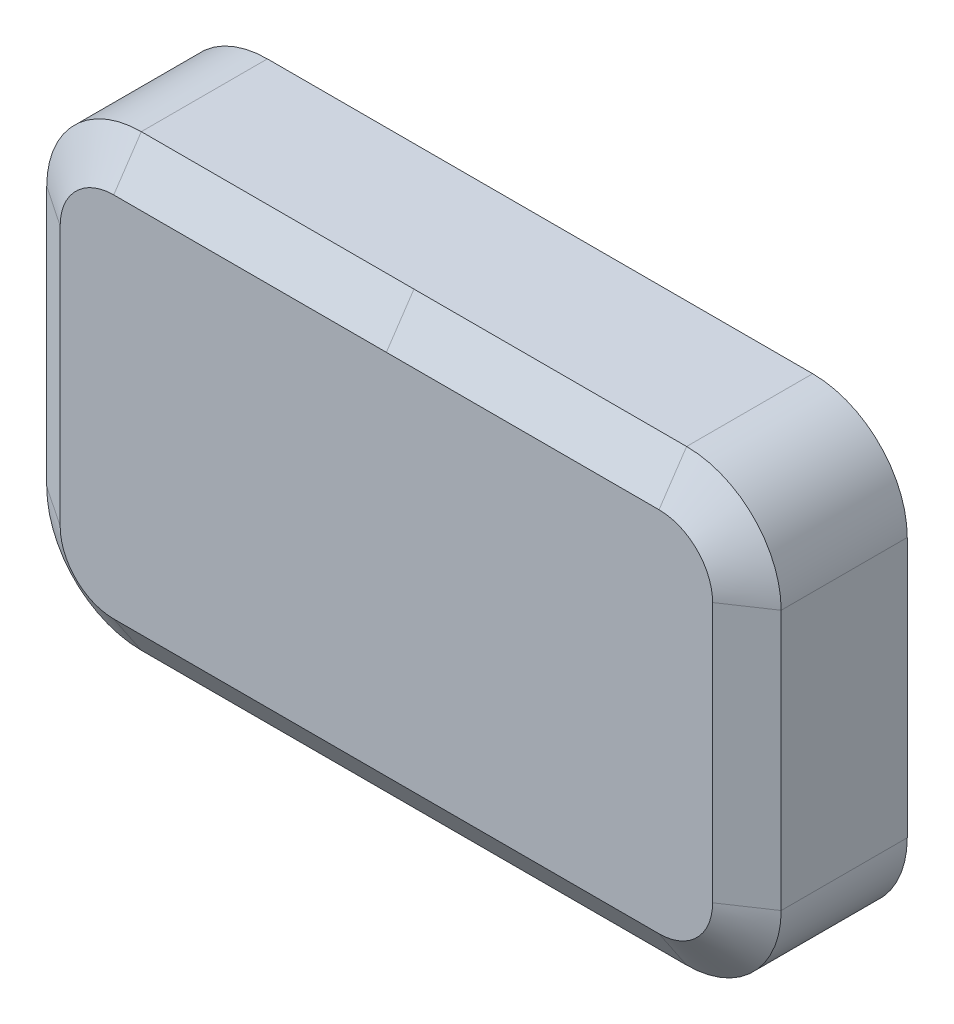
SolidWorks part; units mm, degrees
ref_plane "Front Plane" through (0, 0, 0) normal (0, 0, 1) x (1, 0, 0)
ref_plane "Top Plane" through (0, 0, 0) normal (0, 1, 0) x (1, 0, 0)
ref_plane "Right Plane" through (0, 0, 0) normal (1, 0, 0) x (0, 0, -1)
sketch "Sketch1" plane through (0, 0, 0) normal (0, 0, 1) x (1, 0, 0)
  line L1 (59.182, -36.195) -> (-59.182, -36.195)
  line L2 (59.182, -36.195) -> (59.182, 36.195)
  line L3 (59.182, 36.195) -> (-59.182, 36.195)
  line L4 (-59.182, -36.195) -> (-59.182, 36.195)
  line L5 (59.182, -36.195) -> (-59.182, 36.195) construction
  line L6 (59.182, 36.195) -> (-59.182, -36.195) construction
  point P0 (0, 0)
  dimension "D1" = 118.364
  dimension "D2" = 72.39
extrude "Boss-Extrude1" add sketch "Sketch1" along normal blind 27.94
sketch "Sketch2" plane through (0, 0, 0) normal (0, 0, -1) x (-1, 0, 0)
  line L1 (43.434, -21.717) -> (-43.434, -21.717) construction
  line L2 (43.434, -21.717) -> (43.434, 21.717) construction
  line L3 (43.434, 21.717) -> (-43.434, 21.717) construction
  line L4 (-43.434, -21.717) -> (-43.434, 21.717) construction
  line L5 (43.434, -21.717) -> (-43.434, 21.717) construction
  line L6 (43.434, 21.717) -> (-43.434, -21.717) construction
  circle A0 centre (-43.434, 21.717) radius 4.318
  circle A1 centre (-43.434, -21.717) radius 4.318
  circle A2 centre (43.434, -21.717) radius 4.318
  circle A3 centre (43.434, 21.717) radius 4.318
  point P0 (0, 0)
  point P11 (33.3654, 17.664)
  dimension "D1" = 8.636
  dimension "D2" = 86.868
  dimension "D3" = 43.434
extrude "Boss-Extrude2" add sketch "Sketch2" along normal blind 1.9558 draft 15
fillet "Fillet1" radius 15.24 4 edges at (-59.182, 36.195, 13.97) (-59.182, -36.195, 13.97) (59.182, -36.195, 13.97) (59.182, 36.195, 13.97)
sketch "Sketch3" plane through (0, 0, 0) normal (1, 0, 0) x (0, 0, -1)
  line L0 (-23.495, 36.195) -> (-27.94, 29.591)
  line L1 (-27.94, 36.195) -> (0, 36.195) construction
  line L2 (-27.94, -20.955) -> (-27.94, 20.955) construction
  line L3 (-27.94, 29.591) -> (-27.94, 36.195)
  line L4 (-27.94, 36.195) -> (-23.495, 36.195)
  line L5 (0, 36.195) -> (0, 29.591)
  line L6 (0, -20.955) -> (0, 20.955) construction
  line L7 (0, 29.591) -> (-3.175, 34.417)
  line L8 (-3.175, 34.417) -> (-3.175, 36.195)
  line L9 (-3.175, 36.195) -> (0, 36.195)
  line L10 (0, 0) -> (-27.94, 0) construction
  line L11 (0, 36.195) -> (-27.94, 36.195) construction
  point P17 (-25.1708, 36.195)
  point P18 (0, 0)
  point P19 (4.4531, 36.195)
  point P22 (0, 0)
  dimension "D1" = 59.182
  dimension "D2" = 1.778
  dimension "D3" = 20.32
  dimension "D4" = 3.175
sketch "Sketch4" plane through (0, 0, 27.94) normal (0, 0, 1) x (1, 0, 0)
  line L4 (43.942, 36.195) -> (-43.942, 36.195)
  line L5 (-59.182, 20.955) -> (-59.182, -20.955)
  line L6 (-43.942, -36.195) -> (43.942, -36.195)
  line L7 (59.182, -20.955) -> (59.182, 20.955)
  line L8 (43.942, 36.195) -> (-43.942, 36.195)
  line L9 (-59.182, 20.955) -> (-59.182, -20.955)
  line L10 (-43.942, -36.195) -> (43.942, -36.195)
  line L11 (59.182, -20.955) -> (59.182, 20.955)
  arc A4 (-43.942, 36.195) -> (-59.182, 20.955) centre (-43.942, 20.955) ccw
  arc A5 (-59.182, -20.955) -> (-43.942, -36.195) centre (-43.942, -20.955) ccw
  arc A6 (43.942, -36.195) -> (59.182, -20.955) centre (43.942, -20.955) ccw
  arc A7 (59.182, 20.955) -> (43.942, 36.195) centre (43.942, 20.955) ccw
  arc A8 (-43.942, 36.195) -> (-59.182, 20.955) centre (-43.942, 20.955) ccw
  arc A9 (-59.182, -20.955) -> (-43.942, -36.195) centre (-43.942, -20.955) ccw
  arc A10 (43.942, -36.195) -> (59.182, -20.955) centre (43.942, -20.955) ccw
  arc A11 (59.182, 20.955) -> (43.942, 36.195) centre (43.942, 20.955) ccw
  dimension "D1" = 0
sweep "Cut-Sweep1" cut profiles "Sketch3" path "Sketch4"
sketch "Sketch11" plane through (0, 0, 0) normal (0, 0, -1) x (-1, 0, 0)
  line L0 (-32.512, 6.858) -> (-32.512, -6.858) construction
  line L1 (-26.67, 6.858) -> (-26.67, -6.858)
  line L2 (-38.354, 6.858) -> (-38.354, -6.858)
  line L3 (0, 16.7481) -> (0, 0) construction
  line L4 (32.512, 6.858) -> (32.512, -6.858) construction
  line L5 (26.67, 6.858) -> (26.67, -6.858)
  line L6 (38.354, 6.858) -> (38.354, -6.858)
  arc A0 (-26.67, 6.858) -> (-38.354, 6.858) centre (-32.512, 6.858) ccw
  arc A1 (-38.354, -6.858) -> (-26.67, -6.858) centre (-32.512, -6.858) ccw
  arc A2 (26.67, 6.858) -> (38.354, 6.858) centre (32.512, 6.858) cw
  arc A3 (38.354, -6.858) -> (26.67, -6.858) centre (32.512, -6.858) cw
  point P2 (-32.512, 0)
  point P12 (32.512, 0)
  point P17 (-32.512, 12.7)
  point P18 (-32.512, -12.7)
  point P19 (0, 0)
  dimension "D1" = 53.34
  dimension "D2" = 11.684
  dimension "D3" = 25.4
extrude "Boss-Extrude3" add sketch "Sketch11" along normal blind 1.27
sketch "Sketch12" plane through (0, 0, -1.27) normal (0, 0, -1) x (-1, 0, 0)
  line L0 (-35.052, 6.858) -> (-35.052, 2.8398)
  line L1 (-35.052, -2.8398) -> (-35.052, -6.858)
  line L2 (-29.972, -6.858) -> (-29.972, -2.8398)
  line L3 (-29.972, 2.8398) -> (-29.972, 6.858)
  line L4 (0, 0) -> (0, -8.03) construction
  line L5 (29.972, 2.8398) -> (29.972, 6.858)
  line L6 (29.972, -6.858) -> (29.972, -2.8398)
  line L7 (35.052, -2.8398) -> (35.052, -6.858)
  line L8 (35.052, 6.858) -> (35.052, 2.8398)
  arc A0 (-29.972, 6.858) -> (-35.052, 6.858) centre (-32.512, 6.858) ccw
  arc A1 (-35.052, -6.858) -> (-29.972, -6.858) centre (-32.512, -6.858) ccw
  arc A2 (-35.052, 2.8398) -> (-35.052, -2.8398) centre (-32.512, 0) ccw
  arc A3 (-29.972, -2.8398) -> (-29.972, 2.8398) centre (-32.512, 0) ccw
  arc A4 (29.972, -2.8398) -> (29.972, 2.8398) centre (32.512, 0) cw
  arc A5 (35.052, 2.8398) -> (35.052, -2.8398) centre (32.512, 0) cw
  arc A6 (35.052, -6.858) -> (29.972, -6.858) centre (32.512, -6.858) cw
  arc A7 (29.972, 6.858) -> (35.052, 6.858) centre (32.512, 6.858) cw
  dimension "D1" = 7.62
  dimension "D2" = 5.08
extrude "Cut-Extrude1" cut sketch "Sketch12" against normal blind 4.318
sketch "Sketch13" plane through (0, -36.195, 0) normal (0, -1, 0) x (1, 0, 0)
  line L0 (43.942, 3.175) -> (-43.942, 3.175) construction
  line L1 (-42.7355, 21.1582) -> (29.9085, 21.1582)
  line L2 (-42.7355, 21.1582) -> (-42.7355, 7.9502)
  line L3 (-42.7355, 7.9502) -> (29.9085, 7.9502)
  line L4 (29.9085, 21.1582) -> (29.9085, 7.9502)
  line L5 (33.3883, 19.3802) -> (42.7355, 19.3802)
  line L6 (33.3883, 19.3802) -> (33.3883, 7.9502)
  line L7 (33.3883, 7.9502) -> (42.7355, 7.9502)
  line L8 (42.7355, 19.3802) -> (42.7355, 7.9502)
  line L9 (-43.942, 21.1582) -> (-42.7355, 21.1582) construction
  line L10 (-43.942, 23.495) -> (-43.942, 3.175) construction
  line L11 (43.942, 19.3802) -> (42.7355, 19.3802) construction
  line L12 (43.942, 3.175) -> (43.942, 23.495) construction
  dimension "D1" = 13.208
  dimension "D2" = 72.644
  dimension "D3" = 9.3472
  dimension "D4" = 11.43
  dimension "D5" = 4.7752
  dimension "D6" = 4.7752
  dimension "D7" = 3.4798
extrude "Cut-Extrude2" cut sketch "Sketch13" against normal blind 0.635
